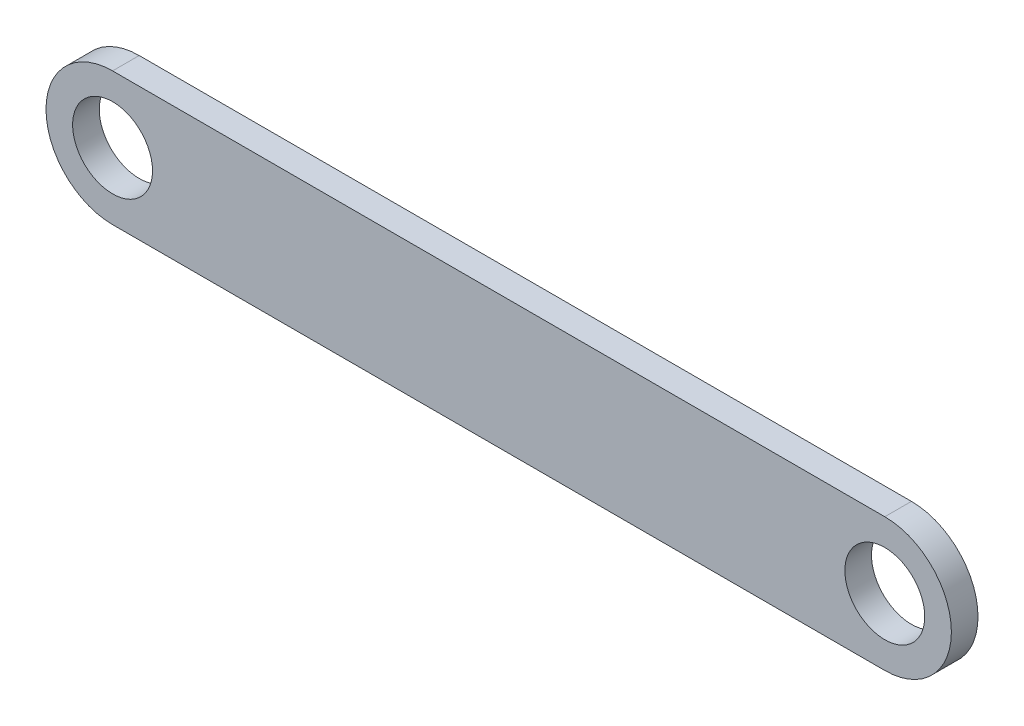
SolidWorks part; units mm, degrees
material "Plain Carbon Steel"
ref_plane "Front Plane" through (0, 0, 0) normal (0, 0, 1) x (1, 0, 0)
ref_plane "Top Plane" through (0, 0, 0) normal (0, 1, 0) x (1, 0, 0)
ref_plane "Right Plane" through (0, 0, 0) normal (1, 0, 0) x (0, 0, -1)
sketch "Sketch1" plane through (0, 0, 0) normal (0, 0, 1) x (1, 0, 0)
  line L0 (0, 0) -> (145, 0) construction
  line L1 (0, 12.5) -> (145, 12.5)
  line L2 (0, -12.5) -> (145, -12.5)
  circle A0 centre (0, 0) radius 7.5
  arc A1 (0, 12.5) -> (0, -12.5) centre (0, 0) ccw
  arc A2 (145, -12.5) -> (145, 12.5) centre (145, 0) ccw
  circle A3 centre (145, 0) radius 7.5
  point P3 (72.5, 0)
  dimension "D1" = 15
  dimension "D2" = 15
  dimension "D3" = 145
  dimension "D4" = 25
extrude "Boss-Extrude1" add sketch "Sketch1" along normal mid plane 5
